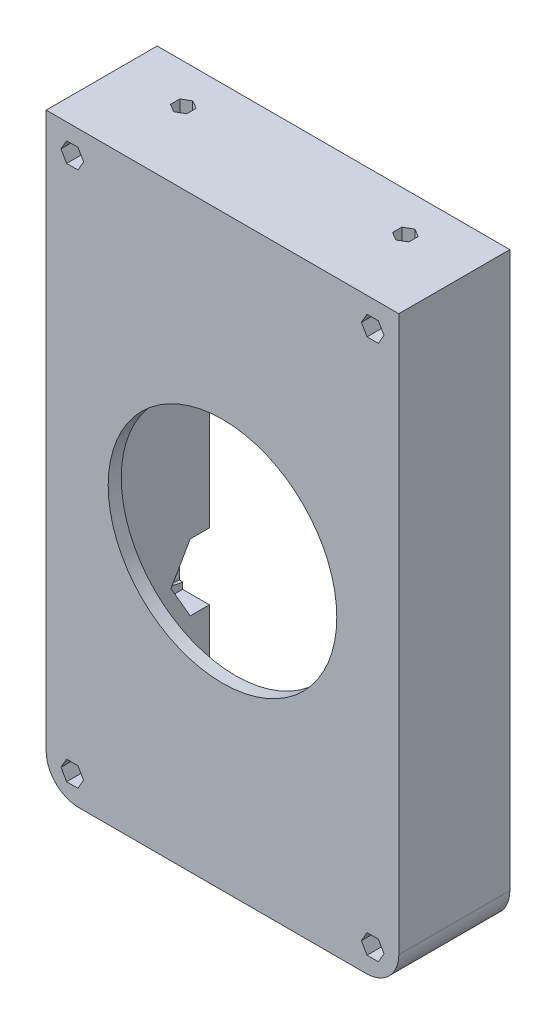
SolidWorks part; units mm, degrees
ref_plane "Front Plane" through (0, 0, 0) normal (0, 0, 1) x (1, 0, 0)
ref_plane "Top Plane" through (0, 0, 0) normal (0, 1, 0) x (1, 0, 0)
ref_plane "Right Plane" through (0, 0, 0) normal (1, 0, 0) x (0, 0, -1)
sketch "Sketch1" plane through (0, 0, 0) normal (0, 0, 1) x (1, 0, 0)
  line L1 (0, 0) -> (54, 0)
  line L2 (0, 0) -> (0, 90)
  line L3 (0, 90) -> (54, 90)
  line L4 (54, 0) -> (54, 90)
  line L5 (8, 82) -> (46, 82)
  line L6 (8, 82) -> (8, 8)
  line L7 (8, 8) -> (46, 8)
  line L8 (46, 82) -> (46, 8)
  dimension "D1" = 90
  dimension "D2" = 54
  dimension "D3" = 8
  dimension "D4" = 8
  dimension "D5" = 8
  dimension "D6" = 8
extrude "Boss-Extrude1" add sketch "Sketch1" along normal blind 30
sketch "Sketch2" plane through (46, 0, 0) normal (-1, 0, 0) x (0, 0, 1)
  line L1 (20.889, 65) -> (17.9445, 70.1)
  line L2 (17.9445, 70.1) -> (12.0555, 70.1)
  line L3 (12.0555, 70.1) -> (9.111, 65)
  line L4 (9.111, 65) -> (12.0555, 59.9)
  line L5 (12.0555, 59.9) -> (17.9445, 59.9)
  line L6 (17.9445, 59.9) -> (20.889, 65)
  line L8 (0, 8) -> (0, 82) construction
  line L10 (20.889, 25) -> (17.9445, 30.1)
  line L11 (17.9445, 30.1) -> (12.0555, 30.1)
  line L12 (12.0555, 30.1) -> (9.111, 25)
  line L13 (9.111, 25) -> (12.0555, 19.9)
  line L14 (12.0555, 19.9) -> (17.9445, 19.9)
  line L15 (17.9445, 19.9) -> (20.889, 25)
  line L16 (12.0555, 70.1) -> (17.9445, 59.9) construction
  line L17 (17.9445, 19.9) -> (12.0555, 30.1) construction
  line L18 (12.0555, 59.9) -> (17.9445, 70.1) construction
  line L19 (0, 45) -> (30, 45) construction
  line L20 (30, 8) -> (30, 82) construction
  circle A0 centre (15, 65) radius 5.1 construction
  circle A1 centre (15, 25) radius 5.1 construction
  dimension "D1" = 20
  dimension "D2" = 15
  dimension "D3" = 10.2
  dimension "D4" = 20
  dimension "D5" = 15
  dimension "D6" = 10.2
extrude "Cut-Extrude1" cut sketch "Sketch2" against normal blind 4.1
sketch "Sketch5" plane through (50.1, 0, 0) normal (-1, 0, 0) x (0, 0, 1)
  line L0 (12.0555, 70.1) -> (17.9445, 59.9) construction
  line L1 (12.0555, 59.9) -> (17.9445, 70.1) construction
  line L3 (12.0555, 19.9) -> (17.9445, 30.1) construction
  line L4 (12.0555, 30.1) -> (17.9445, 19.9) construction
  circle A0 centre (15, 65) radius 4.1
  circle A1 centre (15, 25) radius 4.1
  point P12 (15, 25)
  dimension "D1" = 8.2
  dimension "D2" = 8.2
  dimension "D3" = 0
extrude "Cut-Extrude2" cut sketch "Sketch5" against normal blind 0.5
sketch "Sketch6" plane through (8, 0, 0) normal (1, 0, 0) x (0, 0, -1)
  line L1 (-9.111, 65) -> (-12.0555, 70.1)
  line L2 (-12.0555, 70.1) -> (-17.9445, 70.1)
  line L3 (-17.9445, 70.1) -> (-20.889, 65)
  line L4 (-20.889, 65) -> (-17.9445, 59.9)
  line L5 (-17.9445, 59.9) -> (-12.0555, 59.9)
  line L6 (-12.0555, 59.9) -> (-9.111, 65)
  line L7 (-9.111, 25) -> (-12.0555, 30.1)
  line L8 (-12.0555, 30.1) -> (-17.9445, 30.1)
  line L9 (-17.9445, 30.1) -> (-20.889, 25)
  line L10 (-20.889, 25) -> (-17.9445, 19.9)
  line L11 (-17.9445, 19.9) -> (-12.0555, 19.9)
  line L12 (-12.0555, 19.9) -> (-9.111, 25)
  line L13 (-30, 82) -> (-30, 8) construction
  line L15 (-30, 45) -> (0, 45) construction
  line L16 (0, 82) -> (0, 8) construction
  circle A0 centre (-15, 65) radius 5.1 construction
  circle A1 centre (-15, 25) radius 5.1 construction
  dimension "D1" = 20
  dimension "D2" = 15
  dimension "D3" = 20
  dimension "D4" = 15
  dimension "D5" = 10.2
  dimension "D6" = 10.2
extrude "Cut-Extrude3" cut sketch "Sketch6" against normal blind 4.1
sketch "Sketch7" plane through (3.9, 0, 0) normal (1, 0, 0) x (0, 0, -1)
  line L0 (-30, 82) -> (-30, 8) construction
  line L3 (-17.9445, 59.9) -> (-12.0555, 70.1) construction
  line L4 (-12.0555, 30.1) -> (-17.9445, 19.9) construction
  circle A0 centre (-15, 65) radius 4.1
  circle A1 centre (-15, 25) radius 4.1
  point P10 (-15, 65)
  point P13 (-15, 25)
  dimension "D3" = 8.2
  dimension "D1" = 15
  dimension "D2" = 15
  dimension "D5" = 0
  dimension "D6" = 0
  dimension "D4" = 2
extrude "Cut-Extrude4" cut sketch "Sketch7" against normal blind 0.5
sketch "Sketch8" plane through (0, 0, 30) normal (0, 0, 1) x (1, 0, 0)
  line L1 (0, 90) -> (54, 90)
  line L2 (0, 90) -> (0, 0)
  line L3 (0, 0) -> (54, 0)
  line L4 (54, 90) -> (54, 0)
extrude "Boss-Extrude2" add sketch "Sketch8" along normal blind 2
sketch "Sketch9" plane through (0, 0, 0) normal (0, 0, -1) x (-1, 0, 0)
  line L1 (-54, 90) -> (0, 90)
  line L2 (-54, 90) -> (-54, 0)
  line L3 (-54, 0) -> (0, 0)
  line L4 (0, 90) -> (0, 0)
extrude "Boss-Extrude3" add sketch "Sketch9" along normal blind 2
sketch "Sketch12" plane through (0, 0, -2) normal (0, 0, -1) x (-1, 0, 0)
  line L1 (-54, 90) -> (0, 90)
  line L2 (-54, 90) -> (-54, 0)
  line L3 (-54, 0) -> (0, 0)
  line L4 (0, 90) -> (0, 0)
extrude "Cut-Extrude7" cut sketch "Sketch12" against normal blind 17
sketch "Sketch13" plane through (0, 0, 15) normal (0, 0, -1) x (-1, 0, 0)
  line L0 (0, 90) -> (-54, 90) construction
  line L1 (-48.2679, 86) -> (-49.134, 87.5)
  line L2 (-49.134, 87.5) -> (-50.866, 87.5)
  line L3 (-50.866, 87.5) -> (-51.7321, 86)
  line L4 (-51.7321, 86) -> (-50.866, 84.5)
  line L5 (-50.866, 84.5) -> (-49.134, 84.5)
  line L6 (-49.134, 84.5) -> (-48.2679, 86)
  line L7 (-2.2679, 86) -> (-3.134, 87.5)
  line L8 (-3.134, 87.5) -> (-4.866, 87.5)
  line L9 (-4.866, 87.5) -> (-5.7321, 86)
  line L10 (-5.7321, 86) -> (-4.866, 84.5)
  line L11 (-4.866, 84.5) -> (-3.134, 84.5)
  line L12 (-3.134, 84.5) -> (-2.2679, 86)
  line L13 (0, 0) -> (0, 90) construction
  line L14 (-54, 90) -> (-54, 0) construction
  line L15 (-48.2679, 4) -> (-49.134, 5.5)
  line L16 (-49.134, 5.5) -> (-50.866, 5.5)
  line L17 (-50.866, 5.5) -> (-51.7321, 4)
  line L18 (-51.7321, 4) -> (-50.866, 2.5)
  line L19 (-50.866, 2.5) -> (-49.134, 2.5)
  line L20 (-49.134, 2.5) -> (-48.2679, 4)
  line L21 (-5.7321, 4) -> (-4.866, 2.5)
  line L22 (-4.866, 2.5) -> (-3.134, 2.5)
  line L23 (-3.134, 2.5) -> (-2.2679, 4)
  line L24 (-2.2679, 4) -> (-3.134, 5.5)
  line L25 (-3.134, 5.5) -> (-4.866, 5.5)
  line L26 (-4.866, 5.5) -> (-5.7321, 4)
  circle A0 centre (-50, 86) radius 1.5 construction
  circle A1 centre (-4, 86) radius 1.5 construction
  dimension "D1" = 3
  dimension "D2" = 3
  dimension "D3" = 4
  dimension "D4" = 4
  dimension "D5" = 4
  dimension "D6" = 4
  dimension "D7" = 2
extrude "Cut-Extrude8" cut sketch "Sketch13" against normal through all
sketch "Sketch14" plane through (0, 0, 30) normal (0, 0, -1) x (-1, 0, 0)
  line L0 (-8, 82) -> (-8, 8) construction
  line L1 (-8, 8) -> (-46, 8) construction
  circle A0 centre (-27, 45) radius 17.5
  point P2 (-8, 45)
  dimension "D1" = 35
  dimension "D2" = 19
  dimension "D3" = 37
extrude "Cut-Extrude9" cut sketch "Sketch14" against normal through all
sketch "Sketch15" plane through (0, 90, 0) normal (0, 1, 0) x (1, 0, 0)
  line L0 (54, -32) -> (0, -32) construction
  line L1 (10, -19.5566) -> (8.75, -20.2783)
  line L2 (8.75, -20.2783) -> (8.75, -21.7217)
  line L3 (8.75, -21.7217) -> (10, -22.4434)
  line L4 (10, -22.4434) -> (11.25, -21.7217)
  line L5 (11.25, -21.7217) -> (11.25, -20.2783)
  line L6 (11.25, -20.2783) -> (10, -19.5566)
  line L7 (44, -19.5566) -> (42.75, -20.2783)
  line L8 (42.75, -20.2783) -> (42.75, -21.7217)
  line L9 (42.75, -21.7217) -> (44, -22.4434)
  line L10 (44, -22.4434) -> (45.25, -21.7217)
  line L11 (45.25, -21.7217) -> (45.25, -20.2783)
  line L12 (45.25, -20.2783) -> (44, -19.5566)
  line L13 (54, -32) -> (54, -15) construction
  line L14 (0, -32) -> (0, -15) construction
  circle A0 centre (10, -21) radius 1.25 construction
  circle A1 centre (44, -21) radius 1.25 construction
  dimension "D1" = 2.5
  dimension "D2" = 2.5
  dimension "D3" = 11
  dimension "D4" = 11
  dimension "D5" = 10
  dimension "D6" = 10
extrude "Cut-Extrude10" cut sketch "Sketch15" against normal blind 5
fillet "Fillet1" radius 5 2 edges at (54, 0, 23.5) (0, 0, 23.5)
